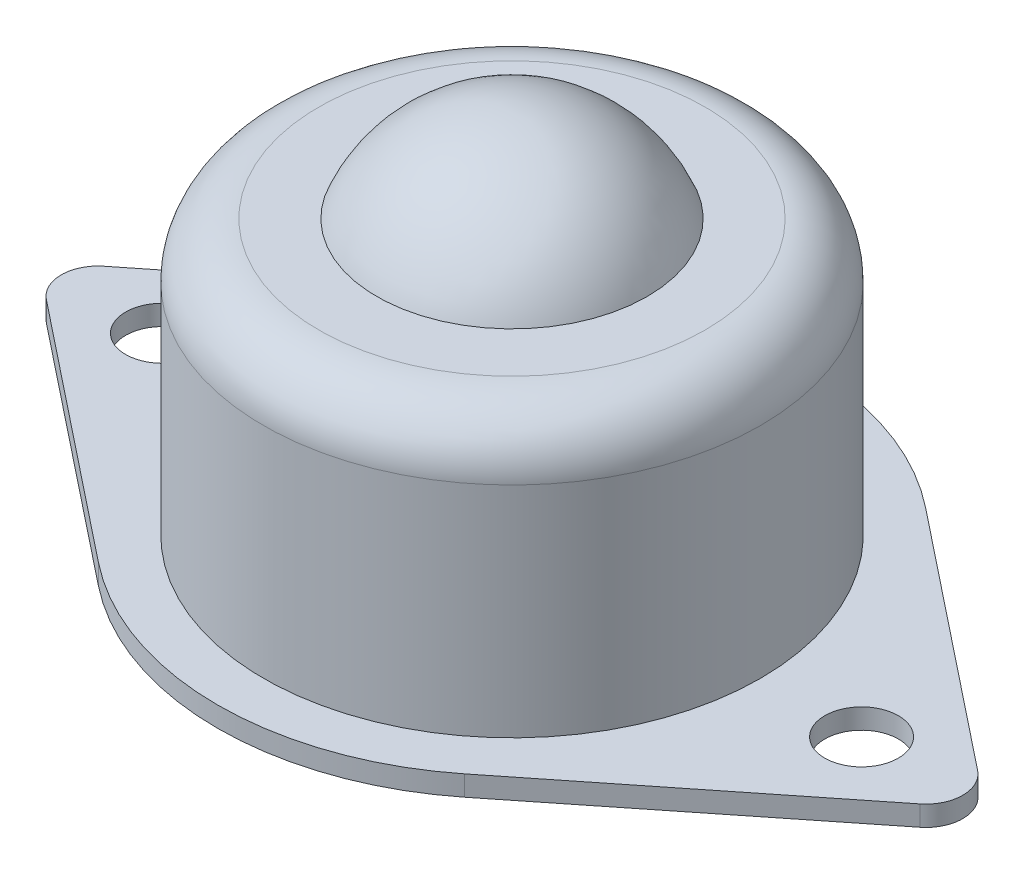
SolidWorks part; units mm, degrees
ref_plane "前视基准面" through (0, 0, 0) normal (0, 0, 1) x (1, 0, 0)
ref_plane "上视基准面" through (0, 0, 0) normal (0, 1, 0) x (1, 0, 0)
ref_plane "右视基准面" through (0, 0, 0) normal (1, 0, 0) x (0, 0, -1)
sketch "草图1" plane through (0, 0, 0) normal (0, 1, 0) x (1, 0, 0)
  line L0 (-49.366, 0) -> (49.366, 0) construction
  line L1 (0, 29.9687) -> (0, 0) construction
  line L2 (-9.9556, 12.5255) -> (-23.7444, 1.5657)
  line L3 (-9.9556, -12.5255) -> (-23.7444, -1.5657)
  line L4 (9.9556, -12.5255) -> (23.7444, -1.5657)
  line L5 (9.9556, 12.5255) -> (23.7444, 1.5657)
  arc A0 (-9.9556, -12.5255) -> (9.9556, -12.5255) centre (0, 0) ccw
  circle A1 centre (-19, 0) radius 2
  arc A2 (-23.7444, 1.5657) -> (-23.7444, -1.5657) centre (-22.5, 0) ccw
  arc A3 (23.7444, 1.5657) -> (23.7444, -1.5657) centre (22.5, 0) cw
  circle A4 centre (19, 0) radius 2
  arc A5 (9.9556, 12.5255) -> (-9.9556, 12.5255) centre (0, 0) ccw
  dimension "D1" = 32
  dimension "D2" = 19
  dimension "D3" = 4
  dimension "D4" = 22.5
extrude "凸台-拉伸1" add sketch "草图1" along normal blind 1.1
sketch "草图2" plane through (0, 0, 0) normal (0, 0, 1) x (1, 0, 0)
  line L0 (0, 22.4224) -> (0, -4.7843) construction
  line L1 (0, 1.1) -> (-13.5, 1.1)
  line L2 (9.9556, 1.1) -> (-9.9556, 1.1) construction
  line L3 (-23.7444, 1.1) -> (-9.9556, 1.1) construction
  line L4 (-13.5, 1.1) -> (-13.5, 13)
  line L5 (-10.5, 16) -> (-7.3485, 16)
  line L6 (-23.7444, 0) -> (-9.9556, 0) construction
  line L7 (0, 21) -> (-9.1531, 21) construction
  line L8 (0, 1.1) -> (0, 21)
  arc A0 (0, 21) -> (-7.3485, 16) centre (0, 13.1) ccw
  arc A1 (-13.5, 13) -> (-10.5, 16) centre (-10.5, 13) cw
  point P19 (-13.5, 16)
  dimension "D3" = 21
  dimension "D4" = 15.8
  dimension "D5" = 3
  dimension "D1" = 16
revolve "旋转1" add sketch "草图2" angle 360 about L8
